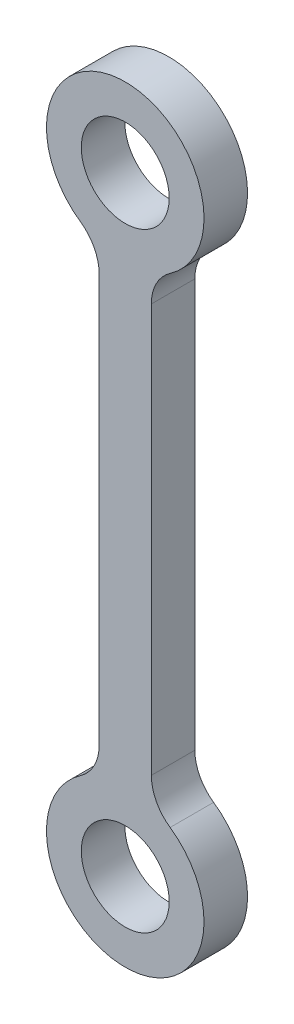
SolidWorks part; units mm, degrees
material "ABS"
ref_plane "Plan de face" through (0, 0, 0) normal (0, 0, 1) x (1, 0, 0)
ref_plane "Plan de dessus" through (0, 0, 0) normal (0, 1, 0) x (1, 0, 0)
ref_plane "Plan de droite" through (0, 0, 0) normal (1, 0, 0) x (0, 0, -1)
sketch "Esquisse1" plane through (0, 0, 0) normal (0, 0, 1) x (1, 0, 0)
  line L0 (0, 0) -> (0, -88.9) construction
  line L1 (-3.81, -14.6685) -> (-3.81, -74.2315)
  line L2 (3.81, -14.6685) -> (3.81, -74.2315)
  circle A0 centre (0, 0) radius 6.4135
  arc A1 (6.5443, -9.4484) -> (-6.5443, -9.4484) centre (0, 0) ccw
  circle A2 centre (0, -88.9) radius 6.4135
  arc A3 (-6.5443, -79.4516) -> (6.5443, -79.4516) centre (0, -88.9) ccw
  arc A4 (3.81, -74.2315) -> (6.5443, -79.4516) centre (10.16, -74.2315) ccw
  arc A5 (-3.81, -74.2315) -> (-6.5443, -79.4516) centre (-10.16, -74.2315) cw
  arc A6 (-3.81, -14.6685) -> (-6.5443, -9.4484) centre (-10.16, -14.6685) ccw
  arc A7 (3.81, -14.6685) -> (6.5443, -9.4484) centre (10.16, -14.6685) cw
  point P11 (3.81, -78.0564)
  point P14 (-3.81, -78.0564)
  point P17 (-3.81, -10.8436)
  point P20 (3.81, -10.8436)
  dimension "D2" = 12.827
  dimension "D3" = 5.08
  dimension "D5" = 6.35
  dimension "D6" = 12.827
  dimension "D1" = 3.81
  dimension "D4" = 88.9
extrude "Boss.-Extru.1" add sketch "Esquisse1" along normal blind 6.35
